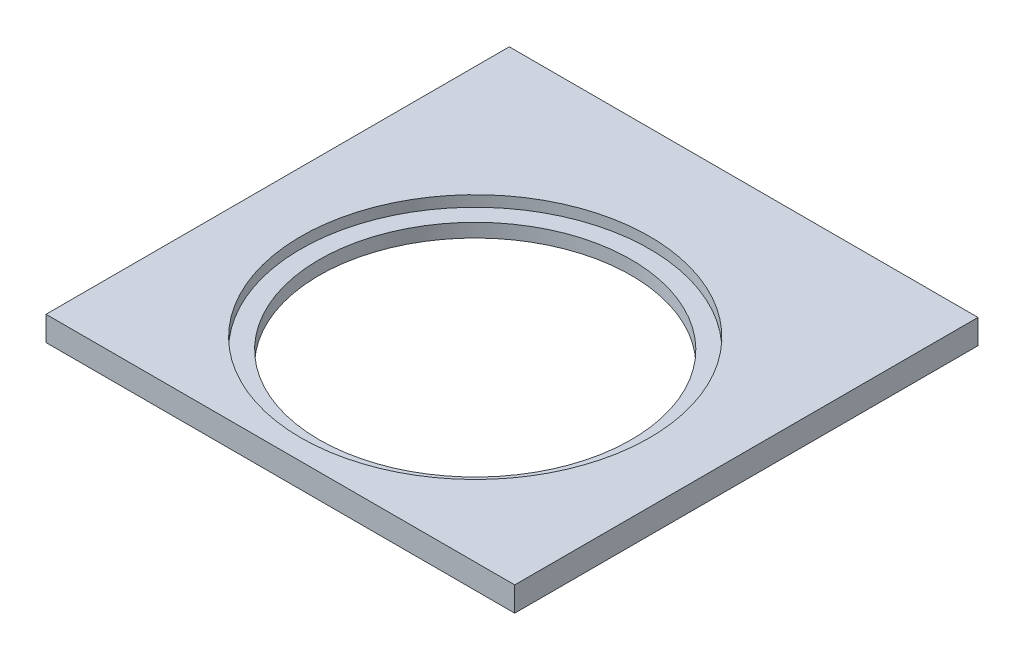
SolidWorks part; units mm, degrees
ref_plane "Спереди" through (0, 0, 0) normal (0, 0, 1) x (1, 0, 0)
ref_plane "Сверху" through (0, 0, 0) normal (0, 1, 0) x (1, 0, 0)
ref_plane "Справа" through (0, 0, 0) normal (1, 0, 0) x (0, 0, -1)
sketch "Эскиз1" plane through (0, 0, 0) normal (0, 1, 0) x (1, 0, 0)
  line L1 (172, -170) -> (-172, -170)
  line L2 (172, -170) -> (172, 170)
  line L3 (172, 170) -> (-172, 170)
  line L4 (-172, -170) -> (-172, 170)
  line L5 (172, -170) -> (-172, 170) construction
  line L6 (172, 170) -> (-172, -170) construction
  point P0 (0, 0)
  dimension "D1" = 340
  dimension "D2" = 344
extrude "Бобышка-Вытянуть1" add sketch "Эскиз1" along normal blind 18
sketch "Эскиз2" plane through (0, 18, 0) normal (0, 1, 0) x (1, 0, 0)
  line L0 (0, -170) -> (0, 170) construction
  line L1 (-172, -170) -> (172, -170) construction
  line L2 (172, 170) -> (-172, 170) construction
  circle A0 centre (0, -27) radius 114.5
  dimension "D1" = 229
  dimension "D2" = 143
extrude "Вырез-Вытянуть1" cut sketch "Эскиз2" against normal through all both and the other way through all
sketch "Эскиз3" plane through (0, 18, 0) normal (0, 1, 0) x (1, 0, 0)
  circle A0 centre (0, -27) radius 128
  dimension "D1" = 256
extrude "Вырез-Вытянуть2" cut sketch "Эскиз3" against normal blind 8
